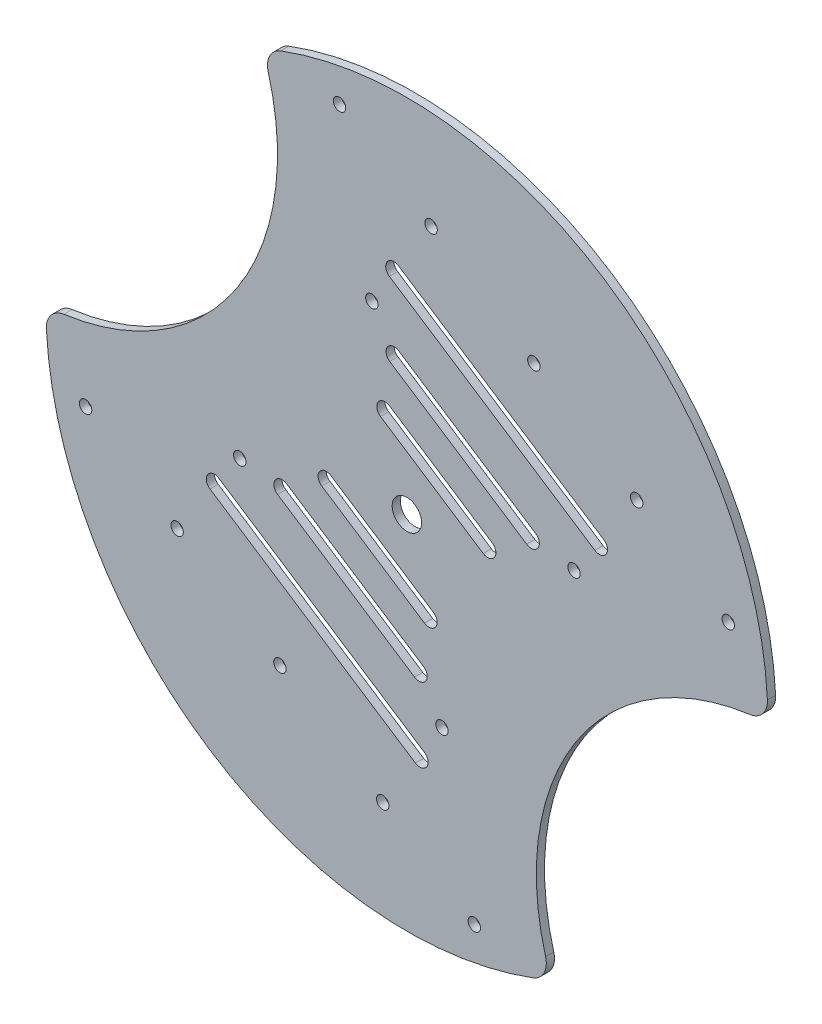
SolidWorks part; units mm, degrees
ref_plane "前视基准面" through (0, 0, 0) normal (0, 0, 1) x (1, 0, 0)
ref_plane "上视基准面" through (0, 0, 0) normal (0, 1, 0) x (1, 0, 0)
ref_plane "右视基准面" through (0, 0, 0) normal (1, 0, 0) x (0, 0, -1)
other "Configuration Table"
sketch "草图1" plane through (0, 0, 0) normal (0, 0, 1) x (1, 0, 0)
  line L0 (-16.4626, 78.5119) -> (-64.8038, 4.7164) construction
  line L1 (-13.5038, 46.6874) -> (-46.9638, 68.6061) construction
  line L2 (-20.6794, 72.0576) -> (-28.4954, 60.0942) construction
  line L3 (-14.5997, 45.0144) -> (-48.0597, 66.9331)
  line L4 (-12.4078, 48.3604) -> (-45.8678, 70.2791)
  line L6 (-11.0753, 59.3328) -> (-36.1703, 75.7718) construction
  line L7 (-12.1712, 57.6598) -> (-37.2662, 74.0988)
  line L8 (-9.9794, 61.0058) -> (-35.0744, 77.4448)
  line L9 (-16.4626, 78.5119) -> (75.5525, 18.2356) construction
  line L11 (-13.286, 28.6132) -> (-63.4761, 61.4912) construction
  line L12 (-14.3819, 26.9402) -> (-64.572, 59.8182)
  line L13 (-12.1901, 30.2862) -> (-62.3801, 63.1642)
  line L15 (13.8944, 88.5122) -> (-19.5656, 110.4308) construction
  line L18 (14.9903, 90.1852) -> (-18.4697, 112.1038)
  line L21 (12.7985, 86.8392) -> (-20.6616, 108.7578)
  line L24 (30.5508, 95.5326) -> (-19.6392, 128.4106) construction
  line L25 (31.6468, 97.2056) -> (-18.5433, 130.0836)
  line L26 (29.4549, 93.8596) -> (-20.7351, 126.7376)
  line L27 (3.2718, 81.2345) -> (-21.8232, 97.6735) construction
  line L28 (4.3678, 82.9075) -> (-20.7272, 99.3465)
  line L29 (2.1759, 79.5615) -> (-22.9191, 96.0005)
  circle A0 centre (-16.4626, 78.5119) radius 80.2193
  circle A1 centre (-16.4626, 78.5119) radius 88.2193
  circle A2 centre (0, 0) radius 1.52
  circle A3 centre (62.0493, 94.9745) radius 1.52
  circle A4 centre (-32.9252, 157.0238) radius 1.52
  circle A5 centre (-94.9745, 62.0493) radius 1.52
  arc A6 (-14.5997, 45.0144) -> (-12.4078, 48.3604) centre (-13.5038, 46.6874) ccw
  arc A7 (-45.8678, 70.2791) -> (-48.0597, 66.9331) centre (-46.9638, 68.6061) ccw
  arc A8 (-12.1712, 57.6598) -> (-9.9794, 61.0058) centre (-11.0753, 59.3328) ccw
  arc A9 (-35.0744, 77.4448) -> (-37.2662, 74.0988) centre (-36.1703, 75.7718) ccw
  arc A10 (-14.3819, 26.9402) -> (-12.1901, 30.2862) centre (-13.286, 28.6132) ccw
  arc A11 (-62.3801, 63.1642) -> (-64.572, 59.8182) centre (-63.4761, 61.4912) ccw
  circle A20 centre (-7.901, 37.6806) radius 1.52
  circle A24 centre (24.3687, 87.0735) radius 1.5174
  circle A30 centre (-25.0242, 119.3432) radius 1.52
  circle A35 centre (-57.2939, 69.9503) radius 1.52
  circle A38 centre (14.562, 125.9992) radius 1.52
  circle A39 centre (-10.553, 142.4075) radius 1.52
  circle A40 centre (39.6771, 109.5908) radius 1.52
  circle A41 centre (-22.3722, 14.6163) radius 1.52
  circle A42 centre (-47.4873, 31.0246) radius 1.52
  circle A43 centre (-72.6023, 47.433) radius 1.52
  arc A44 (71.7567, 78.5119) -> (18.778, -2.363) centre (75.5525, 18.2356) ccw
  arc A45 (14.9903, 90.1852) -> (12.7985, 86.8392) centre (13.8944, 88.5122) cw
  circle A46 centre (-16.4626, 78.5119) radius 3.6
  arc A47 (-20.6616, 108.7578) -> (-18.4697, 112.1038) centre (-19.5656, 110.4308) cw
  arc A48 (31.6468, 97.2056) -> (29.4549, 93.8596) centre (30.5508, 95.5326) cw
  arc A49 (-20.7351, 126.7376) -> (-18.5433, 130.0836) centre (-19.6392, 128.4106) cw
  arc A50 (4.3678, 82.9075) -> (2.1759, 79.5615) centre (3.2718, 81.2345) cw
  arc A51 (-22.9191, 96.0005) -> (-20.7272, 99.3465) centre (-21.8232, 97.6735) cw
  arc A52 (-51.7033, 159.3868) -> (-104.6819, 78.5119) centre (-108.4777, 138.7882) cw
  point P22 (-30.2338, 57.6467)
  point P28 (-23.6228, 67.5523)
  point P36 (68.4544, 8.5898)
  point P40 (-38.381, 45.0522)
  point P45 (71.7567, 78.5119)
  point P46 (0, 0)
  point P47 (86.6155, 10.3803)
  point P52 (-2.8356, 99.4715)
  point P59 (5.4558, 111.9716)
  point P66 (-9.2757, 89.454)
  point P68 (74.4078, 16.5234)
  dimension "D1" = 8
  dimension "D11" = 110
  dimension "D5" = 90
  dimension "D2" = 2
  dimension "D3" = 90
  dimension "D4" = 25
  dimension "D6" = 15
  dimension "D7" = 20
  dimension "D8" = 30
  dimension "D9" = 15
extrude "凸台-拉伸1" add sketch "草图1" along normal blind 2
fillet "圆角1" radius 5 4 edges at (71.7567, 78.5119, 1) (18.778, -2.363, 1) (-104.6819, 78.5119, 1) (-51.7033, 159.3868, 1)
